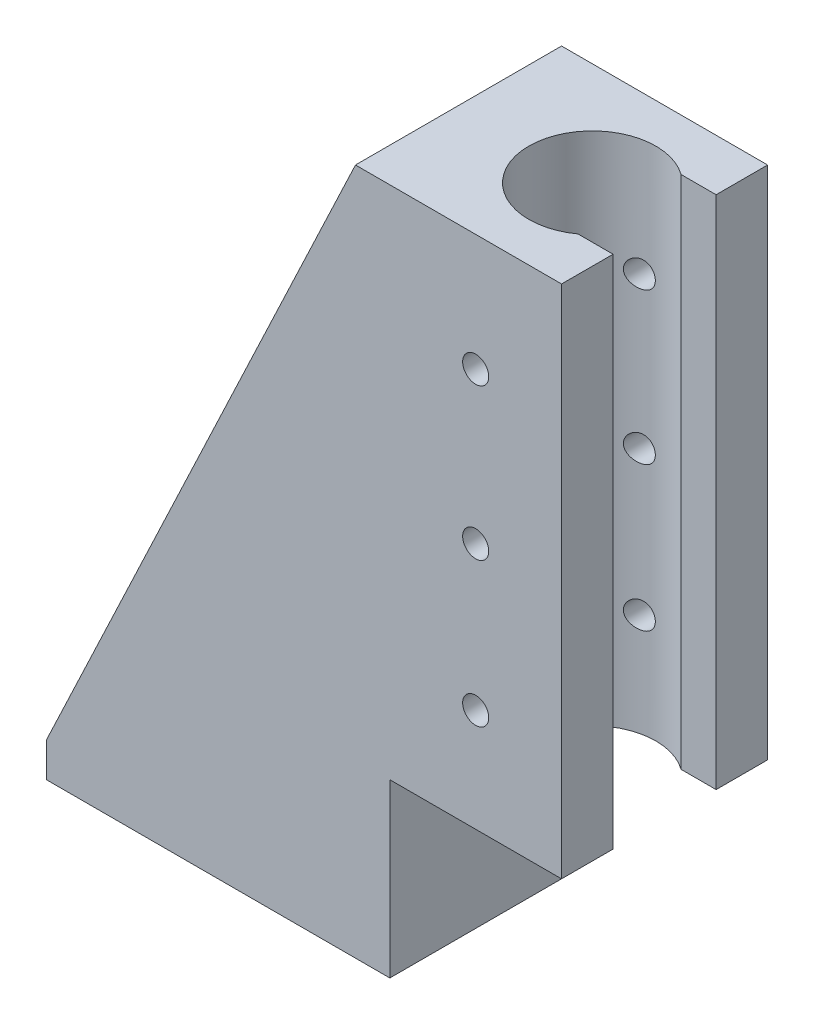
SolidWorks part; units mm, degrees
ref_plane "Front" through (0, 0, 0) normal (0, 0, 1) x (1, 0, 0)
ref_plane "Top" through (0, 0, 0) normal (0, 1, 0) x (1, 0, 0)
ref_plane "Right" through (0, 0, 0) normal (1, 0, 0) x (0, 0, -1)
sketch "Sketch1" plane through (0, 0, 0) normal (0, 0, 1) x (1, 0, 0)
  line L0 (0, 0) -> (63.5, 0)
  line L1 (63.5, 0) -> (63.5, 127)
  line L2 (63.5, 127) -> (57.15, 127)
  line L3 (57.15, 127) -> (57.15, 6.35)
  line L4 (57.15, 6.35) -> (0, 6.35)
  line L5 (0, 6.35) -> (0, 0)
  dimension "D1" = 6.35
  dimension "D2" = 127
  dimension "D3" = 63.5
extrude "Boss-Extrude1" add sketch "Sketch1" along normal mid plane 38.1
sketch "Sketch3" plane through (0, 127, 0) normal (0, 1, 0) x (1, 0, 0)
  line L0 (63.5, -19.05) -> (57.15, -19.05) construction
  line L1 (63.5, 19.05) -> (95.25, 19.05)
  line L2 (63.5, 19.05) -> (63.5, -19.05)
  line L3 (63.5, -19.05) -> (95.25, -19.05)
  line L4 (95.25, 19.05) -> (95.25, -19.05)
  line L5 (88.7677, 9.525) -> (95.25, 9.525)
  line L6 (88.7677, -9.525) -> (95.25, -9.525)
  circle A0 centre (81.8918, 0) radius 11.7475
  circle A1 centre (81.8918, 0) radius 10.9855
  circle A2 centre (81.8918, 0) radius 10.9855 construction
  line M11 (63.5, -19.05) -> (63.5, 19.05)
  dimension "D3" = 31.75
  dimension "D4" = 19.05
  dimension "D1" = 0
  dimension "D2" = 0.762
extrude "Boss-Extrude2" add sketch "Sketch3" against normal blind 95.25 contours A0 L5 L4 L1 L3 L6 M11
sketch "Sketch4" plane through (0, 0, 19.05) normal (0, 0, 1) x (1, 0, 0)
  line L0 (95.25, 127) -> (57.15, 127) construction
  line L1 (63.5, 31.75) -> (95.25, 31.75) construction
  circle A0 centre (79.375, 105.41) radius 2.413
  circle A1 centre (79.375, 50.8) radius 2.413
  circle A2 centre (79.375, 77.47) radius 2.413
  point P9 (79.375, 31.75)
  dimension "D3" = 4.826
  dimension "D4" = 45.72
  dimension "D1" = 21.59
  dimension "D2" = 19.05
extrude "Cut-Extrude1" cut sketch "Sketch4" against normal through all both and the other way through all
sketch "Sketch5" plane through (0, 6.35, 0) normal (0, 1, 0) x (1, 0, 0)
  line L0 (57.15, 19.05) -> (0, 19.05) construction
  line L1 (57.15, -19.05) -> (0, -19.05) construction
  line L2 (0, -19.05) -> (0, 19.05) construction
  line L3 (57.15, -19.05) -> (57.15, 19.05) construction
  circle A0 centre (12.7, 10.16) radius 2.159
  circle A1 centre (44.45, -10.16) radius 2.159
  dimension "D3" = 4.318
  dimension "D1" = 8.89
  dimension "D2" = 8.89
  dimension "D4" = 12.7
  dimension "D5" = 12.7
extrude "Cut-Extrude2" cut sketch "Sketch5" against normal through all both and the other way through all
sketch "Sketch6" plane through (0, 0, 19.05) normal (0, 0, 1) x (1, 0, 0)
  line L0 (57.15, 127) -> (0, 6.35)
  line L9 (0, 6.35) -> (0, 0)
  line L10 (0, 0) -> (63.5, 0)
  line L11 (63.5, 0) -> (63.5, 31.75)
  line L12 (63.5, 31.75) -> (95.25, 31.75)
  line L13 (63.5, 31.75) -> (95.25, 31.75)
  line L14 (95.25, 127) -> (57.15, 127)
  line L15 (57.15, 127) -> (57.15, 6.35)
  line L16 (57.15, 6.35) -> (0, 6.35)
  line L17 (0, 6.35) -> (0, 0)
  line L18 (0, 0) -> (63.5, 0)
  line L19 (63.5, 0) -> (63.5, 31.75)
  line L22 (95.25, 127) -> (57.15, 127)
  line L23 (57.15, 127) -> (57.15, 6.35)
  line L24 (57.15, 6.35) -> (0, 6.35)
  line L25 (95.25, 31.75) -> (95.25, 127)
  line L26 (95.25, 31.75) -> (95.25, 127)
  line M18 (57.15, 127) -> (57.15, 6.35)
  line M19 (57.15, 6.35) -> (0, 6.35)
  dimension "D1" = 0
extrude "Boss-Extrude3" add sketch "Sketch6" against normal blind 3.175 contours L0 M18 M19
mirror "Mirror1" about plane through (0, 0, 0) normal (0, 0, 1) of "Boss-Extrude3"
fillet "Fillet1" radius 6.35 1 edges at (57.15, 6.35, 0)
fillet "Fillet2" radius 3.175 6 edges at (25.4, 6.35, 15.875) (55.2901, 8.2099, 15.875) (25.4, 6.35, -15.875) (55.2901, 8.2099, -15.875) (57.15, 69.85, 15.875) (57.15, 69.85, -15.875)
